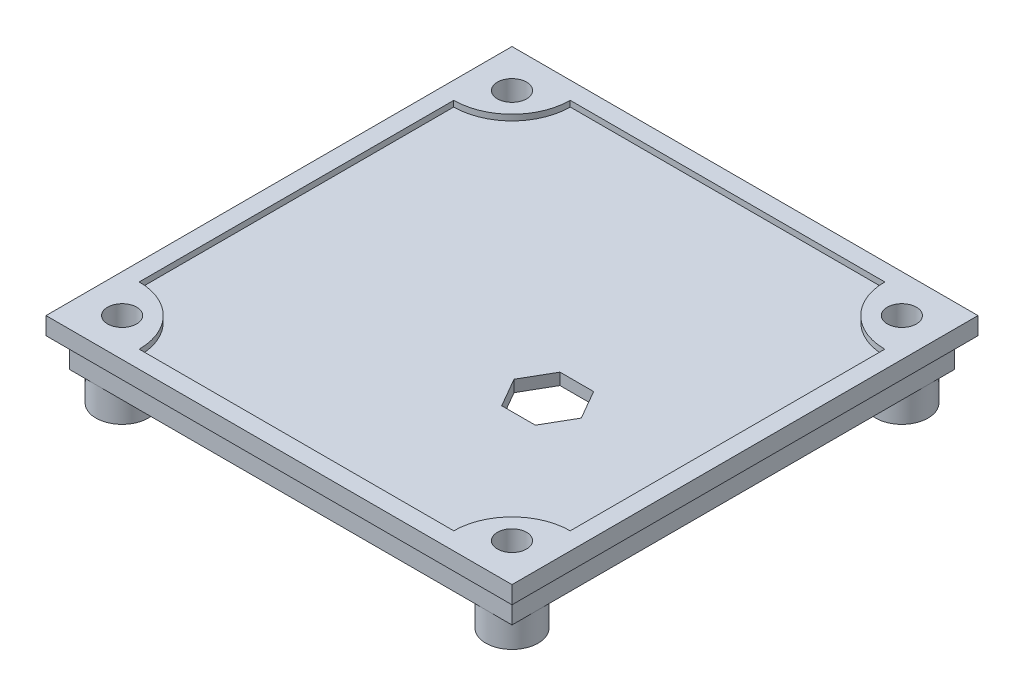
SolidWorks part; units mm, degrees
ref_plane "Front Plane" through (0, 0, 0) normal (0, 0, 1) x (1, 0, 0)
ref_plane "Top Plane" through (0, 0, 0) normal (0, 1, 0) x (1, 0, 0)
ref_plane "Right Plane" through (0, 0, 0) normal (1, 0, 0) x (0, 0, -1)
sketch "Sketch2" plane through (0, 0, 0) normal (0, 1, 0) x (1, 0, 0)
  line L1 (-40, 40) -> (40, 40)
  line L2 (-40, 40) -> (-40, -40)
  line L3 (-40, -40) -> (40, -40)
  line L4 (40, 40) -> (40, -40)
  line L5 (-40, 40) -> (40, -40) construction
  line L6 (-40, -40) -> (40, 40) construction
  point P0 (0, 0)
  dimension "D1" = 80
  dimension "D2" = 80
extrude "Boss-Extrude1" add sketch "Sketch2" against normal blind 3
sketch "Sketch3" plane through (0, 0, 0) normal (0, 1, 0) x (1, 0, 0)
  line L0 (-27, 37) -> (27, 37)
  line L5 (-37, 37) -> (37, -37) construction
  line L6 (-37, -37) -> (37, 37) construction
  line L8 (37, 27) -> (37, -27)
  line L9 (27, -37) -> (-27, -37)
  line L10 (-37, -27) -> (-37, 27)
  arc A0 (-27, 37) -> (-37, 27) centre (-37, 37) cw
  arc A1 (37, 27) -> (27, 37) centre (37, 37) cw
  arc A2 (-27, -37) -> (-37, -27) centre (-37, -37) ccw
  arc A3 (27, -37) -> (37, -27) centre (37, -37) cw
  point P0 (0, 0)
extrude "Cut-Extrude1" cut sketch "Sketch3" against normal blind 1
sketch "Sketch4" plane through (0, 0, 0) normal (0, 1, 0) x (1, 0, 0)
  circle A0 centre (33.4645, 33.4645) radius 2.5
  circle A1 centre (-33.4645, 33.4645) radius 2.5
  circle A2 centre (-33.4645, -33.4645) radius 2.5
  circle A3 centre (33.4645, -33.4645) radius 2.5
sketch "Sketch5" plane through (0, -3, 0) normal (0, -1, 0) x (1, 0, 0)
  line L1 (-38, 38) -> (38, 38)
  line L2 (-38, 38) -> (-38, -38)
  line L3 (-38, -38) -> (38, -38)
  line L4 (38, 38) -> (38, -38)
  line L5 (-38, 38) -> (38, -38) construction
  line L6 (-38, -38) -> (38, 38) construction
  point P0 (0, 0)
  dimension "D1" = 76
  dimension "D2" = 76
extrude "Boss-Extrude2" add sketch "Sketch5" along normal blind 5
sketch "Sketch6" plane through (0, -8, 0) normal (0, -1, 0) x (1, 0, 0)
  line L1 (-37, 37) -> (37, 37)
  line L2 (-37, 37) -> (-37, -37)
  line L3 (-37, -37) -> (37, -37)
  line L4 (37, 37) -> (37, -37)
  line L5 (-37, 37) -> (37, -37) construction
  line L6 (-37, -37) -> (37, 37) construction
  point P0 (0, 0)
  dimension "D1" = 74
  dimension "D2" = 74
extrude "Cut-Extrude2" cut sketch "Sketch6" against normal blind 5
sketch "Sketch7" plane through (0, -3, 0) normal (0, -1, 0) x (1, 0, 0)
  circle A0 centre (-33.4645, 33.4645) radius 4.5
  circle A1 centre (33.4645, 33.4645) radius 4.5
  circle A2 centre (-33.4645, -33.4645) radius 4.5
  circle A3 centre (33.4645, -33.4645) radius 4.5
extrude "Boss-Extrude3" add sketch "Sketch7" along normal blind 10
extrude "Cut-Extrude8" cut sketch "Sketch4" against normal blind 13
sketch "Sketch9" plane through (0, -3, 0) normal (0, -1, 0) x (1, 0, 0)
  line L0 (-7, 41.4745) -> (-7, 24) construction
  line L1 (-7, 24) -> (-37, 24) construction
  line L2 (-37, 30.6806) -> (-37, -30.6806) construction
  line L3 (30.6806, 37) -> (-30.6806, 37) construction
  circle A0 centre (-7, 24) radius 3
  circle A1 centre (-7, 24) radius 2
  dimension "D1" = 13
  dimension "D2" = 30
extrude "Boss-Extrude4" add sketch "Sketch9" along normal blind 5
sketch "Sketch10" plane through (0, -3, 0) normal (0, -1, 0) x (1, 0, 0)
  line L0 (-9, -10) -> (-9, -17) construction
  line L1 (-8.5, -10) -> (-8.5, -17)
  line L2 (-9.5, -10) -> (-9.5, -17)
  line L3 (-37, 30.6806) -> (-37, -30.6806) construction
  line L4 (-30.6806, -37) -> (30.6806, -37) construction
  line L5 (30.6806, 37) -> (-30.6806, 37) construction
  line L6 (12.5, -10) -> (12.5, -17) construction
  line L7 (13, -10) -> (13, -17)
  line L8 (12, -10) -> (12, -17)
  line L9 (37, -30.6806) -> (37, 30.6806) construction
  arc A0 (-8.5, -10) -> (-9.5, -10) centre (-9, -10) ccw
  arc A1 (-9.5, -17) -> (-8.5, -17) centre (-9, -17) ccw
  arc A2 (13, -10) -> (12, -10) centre (12.5, -10) ccw
  arc A3 (12, -17) -> (13, -17) centre (12.5, -17) ccw
  point P2 (-9, -13.5)
  point P15 (12.5, -13.5)
  dimension "D1" = 28
  dimension "D5" = 20
  dimension "D2" = 20
  dimension "D3" = 47
  dimension "D4" = 24
extrude "Boss-Extrude5" add sketch "Sketch10" along normal blind 5
sketch "Sketch11" plane through (0, -1, 0) normal (0, 1, 0) x (1, 0, 0)
  line L1 (17.3004, -3.292) -> (11.5269, -3.292)
  line L2 (11.5269, -3.292) -> (8.6402, -8.292)
  line L3 (8.6402, -8.292) -> (11.5269, -13.292)
  line L4 (11.5269, -13.292) -> (17.3004, -13.292)
  line L5 (17.3004, -13.292) -> (20.1872, -8.292)
  line L6 (20.1872, -8.292) -> (17.3004, -3.292)
  circle A0 centre (14.4137, -8.292) radius 5 construction
extrude "Cut-Extrude9" cut sketch "Sketch11" against normal blind 10
